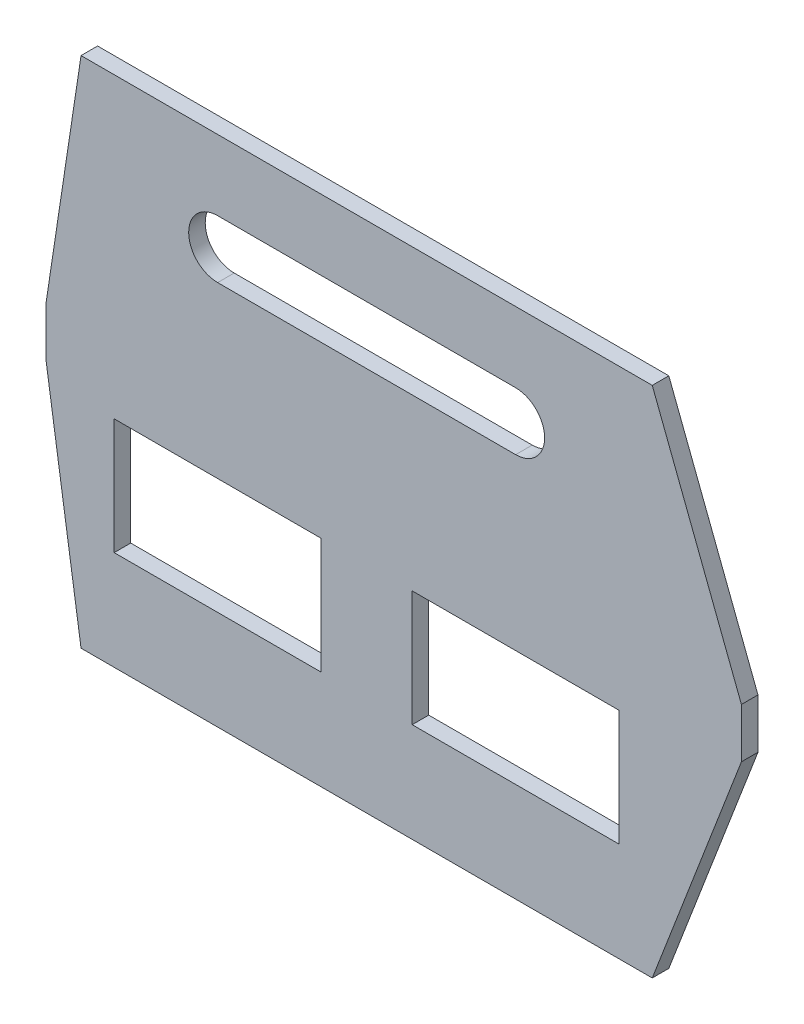
SolidWorks part; units mm, degrees
ref_plane "Front Plane" through (0, 0, 0) normal (0, 0, 1) x (1, 0, 0)
ref_plane "Top Plane" through (0, 0, 0) normal (0, 1, 0) x (1, 0, 0)
ref_plane "Right Plane" through (0, 0, 0) normal (1, 0, 0) x (0, 0, -1)
sketch "Sketch4" plane through (0, 0, 0) normal (0, 0, 1) x (1, 0, 0)
  line L0 (0, 0) -> (-345, 0)
  line L1 (-345, 0) -> (-366.1484, 140)
  line L2 (-366.1484, 140) -> (-366.1484, 170)
  line L3 (-366.1484, 170) -> (-345, 310)
  line L4 (-345, 310) -> (0, 310)
  line L5 (0, 310) -> (53.8516, 170)
  line L6 (53.8516, 170) -> (53.8516, 140)
  line L7 (53.8516, 140) -> (0, 0)
  line L8 (-262.5, 250) -> (-82.5, 250) construction
  line L9 (-262.5, 267.5) -> (-82.5, 267.5)
  line L10 (-262.5, 232.5) -> (-82.5, 232.5)
  line L12 (-325, 130) -> (-200, 130)
  line L13 (-325, 130) -> (-325, 60)
  line L14 (-325, 60) -> (-200, 60)
  line L15 (-200, 130) -> (-200, 60)
  line L16 (-20, 130) -> (-145, 130)
  line L17 (-20, 130) -> (-20, 60)
  line L18 (-20, 60) -> (-145, 60)
  line L19 (-145, 130) -> (-145, 60)
  arc A0 (-262.5, 267.5) -> (-262.5, 232.5) centre (-262.5, 250) ccw
  arc A1 (-82.5, 232.5) -> (-82.5, 267.5) centre (-82.5, 250) ccw
  point P3 (-172.5, 250)
  point P25 (-26.9159, 21.7117)
  dimension "D12" = 172.5
  dimension "D14" = 17.5
  dimension "D1" = 310
  dimension "D2" = 140
  dimension "D3" = 140
  dimension "D4" = 140
  dimension "D5" = 140
  dimension "D6" = 345
  dimension "D7" = 345
  dimension "D8" = 420
  dimension "D9" = 150
  dimension "D10" = 150
  dimension "D11" = 60
  dimension "D13" = 180
  dimension "D15" = 20
  dimension "D16" = 20
  dimension "D17" = 60
  dimension "D18" = 60
  dimension "D19" = 70
  dimension "D20" = 125
  dimension "D21" = 70
  dimension "D22" = 125
extrude "Boss-Extrude1" add sketch "Sketch4" along normal blind 10
